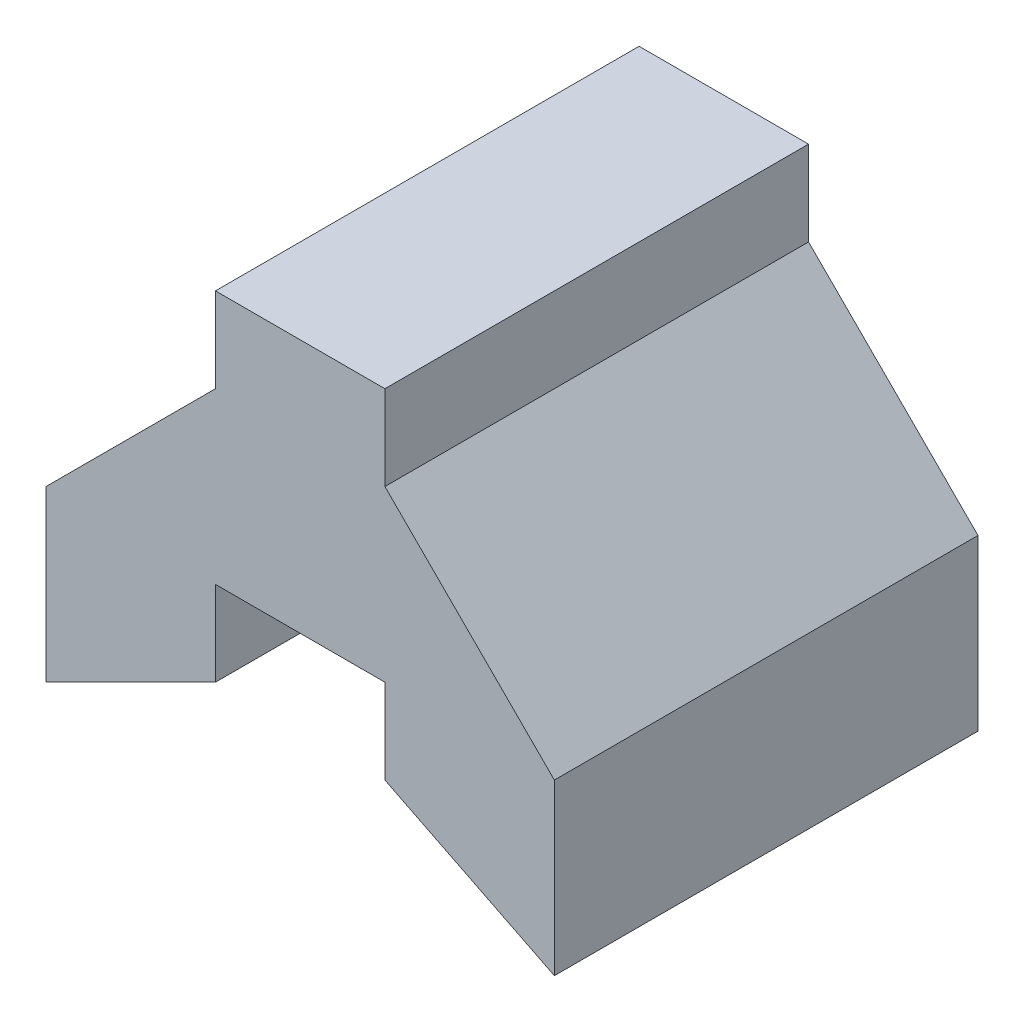
SolidWorks part; units mm, degrees
ref_plane "Front Plane" through (0, 0, 0) normal (0, 0, 1) x (1, 0, 0)
ref_plane "Top Plane" through (0, 0, 0) normal (0, 1, 0) x (1, 0, 0)
ref_plane "Right Plane" through (0, 0, 0) normal (1, 0, 0) x (0, 0, -1)
sketch "Sketch1" plane through (0, 0, 0) normal (0, 0, 1) x (1, 0, 0)
  line L0 (0, 0) -> (-2, 0)
  line L1 (-2, 0) -> (-4, -1)
  line L2 (-4, -1) -> (-4, 1)
  line L3 (-4, 1) -> (-2, 3)
  line L4 (-2, 3) -> (-2, 4)
  line L5 (-2, 4) -> (0, 4)
  line L6 (0, 4) -> (0, 3)
  line L7 (0, 3) -> (2, 1)
  line L8 (2, 1) -> (2, -1)
  line L9 (2, -1) -> (0, 0)
  dimension "D1" = 2
  dimension "D2" = 2
  dimension "D3" = 1
  dimension "D4" = 2
  dimension "D5" = 1
  dimension "D6" = 2
  dimension "D7" = 2
  dimension "D8" = 2
  dimension "D9" = 2
extrude "Boss-Extrude1" add sketch "Sketch1" along normal blind 5
sketch "Sketch2" plane through (0, 0, 5) normal (0, 0, 1) x (1, 0, 0)
  line L0 (0, 1) -> (-2, 1)
  line L1 (-2, 0) -> (0, 0) construction
  dimension "D1" = 1
ref_plane "Plane1" through (0, 0, 0) normal (0, -0.9806, 0.1961) x (-1, 0, 0)
sketch "Sketch3" plane through (0, 0, 0) normal (0, -0.9806, 0.1961) x (-1, 0, 0)
  line L0 (2, 0) -> (2, -5.099)
  line L1 (2, -5.099) -> (0, -5.099)
  line L2 (0, -5.099) -> (0, 0)
  line L3 (0, 0) -> (2, 0)
extrude "Cut-Extrude3" cut sketch "Sketch3" along normal blind 2
